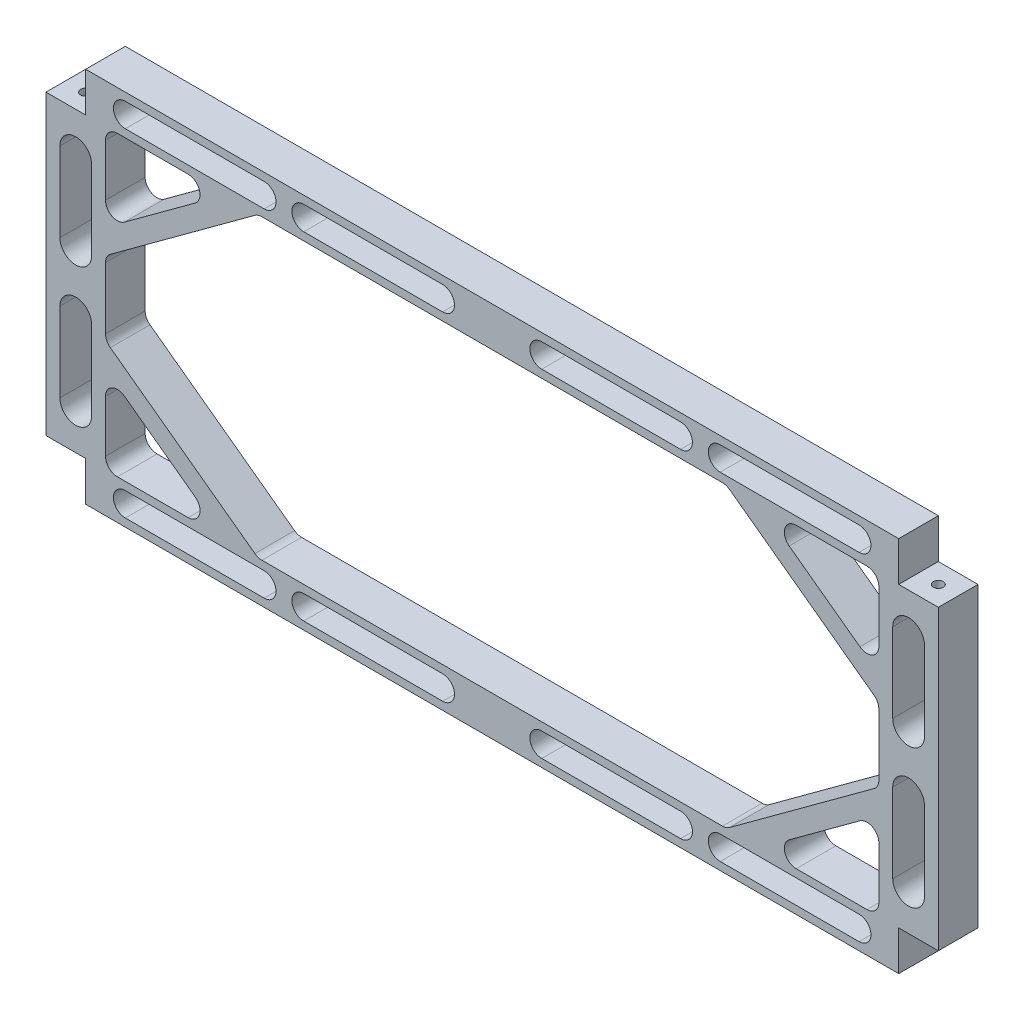
SolidWorks part; units mm, degrees
material "2014 Alloy"
ref_plane "Front Plane" through (0, 0, 0) normal (0, 0, 1) x (1, 0, 0)
ref_plane "Top Plane" through (0, 0, 0) normal (0, 1, 0) x (1, 0, 0)
ref_plane "Right Plane" through (0, 0, 0) normal (1, 0, 0) x (0, 0, -1)
sketch "Sketch1" plane through (0, 0, 0) normal (0, 0, 1) x (1, 0, 0)
  line L0 (0, 0) -> (225, 0)
  line L1 (225, 0) -> (225, 95)
  line L2 (225, 95) -> (0, 95)
  line L3 (0, 95) -> (0, 0)
  line L4 (15, 85) -> (15, 10)
  line L5 (15, 10) -> (210, 10)
  line L6 (210, 10) -> (210, 85)
  line L7 (210, 85) -> (15, 85)
  line L8 (15, 63) -> (45, 85)
  line L9 (0, 47.5) -> (225, 47.5) construction
  line L10 (112.5, 95) -> (112.5, 0) construction
  line L11 (15, 56.7996) -> (53.455, 85)
  line L12 (15, 32) -> (45, 10)
  line L13 (15, 38.2004) -> (53.455, 10)
  line L14 (210, 63) -> (180, 85)
  line L15 (210, 56.7996) -> (171.545, 85)
  line L16 (210, 32) -> (180, 10)
  line L17 (210, 38.2004) -> (171.545, 10)
  line L18 (225, 85) -> (215, 85)
  line L19 (215, 85) -> (215, 95)
  line L20 (225, 10) -> (215, 10)
  line L21 (215, 10) -> (215, 0)
  line L22 (0, 85) -> (10, 85)
  line L23 (10, 85) -> (10, 95)
  line L24 (0, 10) -> (10, 10)
  line L25 (10, 10) -> (10, 0)
  line L26 (217.5, 75) -> (217.5, 55) construction
  line L27 (217.5, 40) -> (217.5, 20) construction
  line L28 (213.5, 75) -> (213.5, 55)
  line L29 (213.5, 40) -> (213.5, 20)
  line L30 (221.5, 75) -> (221.5, 55)
  line L31 (221.5, 40) -> (221.5, 20)
  line L32 (205, 90) -> (170, 90) construction
  line L33 (160, 90) -> (125, 90) construction
  line L34 (100, 90) -> (65, 90) construction
  line L35 (55, 90) -> (20, 90) construction
  line L36 (205, 93) -> (170, 93)
  line L37 (160, 93) -> (125, 93)
  line L38 (100, 93) -> (65, 93)
  line L39 (55, 93) -> (20, 93)
  line L40 (205, 87) -> (170, 87)
  line L41 (160, 87) -> (125, 87)
  line L42 (100, 87) -> (65, 87)
  line L43 (55, 87) -> (20, 87)
  line L44 (55, 8) -> (20, 8)
  line L45 (55, 2) -> (20, 2)
  line L46 (100, 8) -> (65, 8)
  line L47 (100, 2) -> (65, 2)
  line L48 (160, 2) -> (125, 2)
  line L49 (160, 8) -> (125, 8)
  line L50 (205, 2) -> (170, 2)
  line L51 (205, 8) -> (170, 8)
  line L52 (3.5, 75) -> (3.5, 55)
  line L53 (11.5, 75) -> (11.5, 55)
  line L54 (3.5, 40) -> (3.5, 20)
  line L55 (11.5, 40) -> (11.5, 20)
  arc A0 (213.5, 75) -> (221.5, 75) centre (217.5, 75) cw
  arc A1 (213.5, 55) -> (221.5, 55) centre (217.5, 55) ccw
  arc A2 (213.5, 40) -> (221.5, 40) centre (217.5, 40) cw
  arc A3 (213.5, 20) -> (221.5, 20) centre (217.5, 20) ccw
  arc A4 (205, 93) -> (205, 87) centre (205, 90) cw
  arc A5 (170, 93) -> (170, 87) centre (170, 90) ccw
  arc A6 (160, 93) -> (160, 87) centre (160, 90) cw
  arc A7 (125, 93) -> (125, 87) centre (125, 90) ccw
  arc A8 (100, 93) -> (100, 87) centre (100, 90) cw
  arc A9 (65, 93) -> (65, 87) centre (65, 90) ccw
  arc A10 (55, 93) -> (55, 87) centre (55, 90) cw
  arc A11 (20, 93) -> (20, 87) centre (20, 90) ccw
  arc A12 (20, 2) -> (20, 8) centre (20, 5) cw
  arc A13 (55, 2) -> (55, 8) centre (55, 5) ccw
  arc A14 (65, 2) -> (65, 8) centre (65, 5) cw
  arc A15 (100, 2) -> (100, 8) centre (100, 5) ccw
  arc A16 (125, 2) -> (125, 8) centre (125, 5) cw
  arc A17 (160, 2) -> (160, 8) centre (160, 5) ccw
  arc A18 (205, 2) -> (205, 8) centre (205, 5) ccw
  arc A19 (170, 2) -> (170, 8) centre (170, 5) cw
  arc A20 (11.5, 75) -> (3.5, 75) centre (7.5, 75) ccw
  arc A21 (11.5, 55) -> (3.5, 55) centre (7.5, 55) cw
  arc A22 (11.5, 40) -> (3.5, 40) centre (7.5, 40) ccw
  arc A23 (11.5, 20) -> (3.5, 20) centre (7.5, 20) cw
  dimension "D1" = 95
  dimension "D2" = 225
  dimension "D3" = 10
  dimension "D4" = 15
  dimension "D5" = 10
  dimension "D6" = 15
  dimension "D7" = 30
  dimension "D8" = 22
  dimension "D9" = 5
  dimension "D10" = 10
  dimension "D11" = 10
  dimension "D12" = 7.5
  dimension "D13" = 20
  dimension "D14" = 20
  dimension "D15" = 10
  dimension "D16" = 10
  dimension "D19" = 35
  dimension "D20" = 35
  dimension "D21" = 10
  dimension "D22" = 10
  dimension "D23" = 35
  dimension "D24" = 35
  dimension "D25" = 10
  dimension "D26" = 10
  dimension "D27" = 5
  dimension "D17" = 4
  dimension "D18" = 4
  dimension "D28" = 3
  dimension "D29" = 3
extrude "Boss-Extrude1" add sketch "Sketch1" along normal blind 10 contours L2 L3 L0 L1 L7 L6 L5 L4 | L4 L11 L7 L8 | L13 L4 L12 L5 | L6 L17 L5 L16 | L15 L6 L14 L7
fillet "Fillet1" radius 3 20 edges at (180, 85, 5) (210, 63, 5) (210, 85, 5) (171.545, 85, 5) (210, 32, 5) (180, 10, 5) (210, 56.7996, 5) (210, 38.2004, 5) (171.545, 10, 5) (210, 10, 5) (45, 10, 5) (15, 32, 5) (15, 10, 5) (53.455, 10, 5) (15, 38.2004, 5) (15, 56.7996, 5) (53.455, 85, 5) (45, 85, 5) (15, 63, 5) (15, 85, 5)
hole_wizard "M3 Tapped Hole2" positions "Sketch5" profile "Sketch4" tap size "M3" standard "ISO"
sketch "Sketch5" plane through (0, 85, 0) normal (0, 1, 0) x (1, 0, 0)
  line L0 (0, 0) -> (10, 0) construction
  line L1 (10, -10) -> (10, 0) construction
  line L2 (215, -10) -> (215, 0) construction
  point P0 (220, -5)
  point P2 (5, -5)
  dimension "D1" = 5
  dimension "D2" = 5
  dimension "D3" = 5
sketch "Sketch4" plane through (220, 85, 5) normal (1, 0, 0) x (0, 0, 1)
  line L0 (0, 0) -> (0, 15.7511)
  line L1 (0, 15.7511) -> (1.25, 15)
  line L2 (1.25, 15) -> (1.25, 0)
  line L5 (1.25, 0) -> (0, 0)
  line L10 (0, 15.7511) -> (-1.25, 15) construction
  line L11 (0, -6.35) -> (0, 107.95) construction
  dimension "Tap Drill Dia." = 2.5
  dimension "Tap Drill Depth" = 15
  dimension "Drill Angle" = 118
cosmetic thread "Hole Thread3" parameters "D1"=8.6081, "D2"=3
cosmetic thread "Hole Thread4" parameters "D1"=8.6081, "D2"=3
